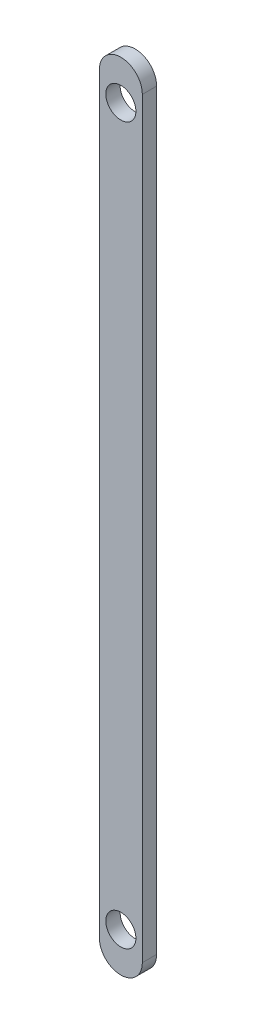
SolidWorks part; units mm, degrees
material "5052-O"
ref_plane "前基準面" through (0, 0, 0) normal (0, 0, 1) x (1, 0, 0)
ref_plane "上基準面" through (0, 0, 0) normal (0, 1, 0) x (1, 0, 0)
ref_plane "右基準面" through (0, 0, 0) normal (1, 0, 0) x (0, 0, -1)
sketch "草圖1" plane through (0, 0, 0) normal (0, 0, 1) x (1, 0, 0)
  line L0 (-3, -52.5) -> (-3, 52.5)
  line L1 (3, -52.5) -> (3, 52.5)
  line L2 (-3, 0) -> (3, 0) construction
  arc A0 (-3, 52.5) -> (3, 52.5) centre (0, 52.5) cw
  arc A1 (-3, -52.5) -> (3, -52.5) centre (0, -52.5) ccw
  dimension "D4" = 3
  dimension "D1" = 6
  dimension "D2" = 105
extrude "填料-伸長1" add sketch "草圖1" along normal blind 2
sketch "草圖2" plane through (0, 0, 2) normal (0, 0, 1) x (1, 0, 0)
  line L0 (0, 50) -> (0, -50) construction
  circle A0 centre (0, 50) radius 2.1
  circle A1 centre (0, -50) radius 2.1
  dimension "D2" = 4.2
  dimension "D1" = 100
extrude "除料-伸長1" cut sketch "草圖2" against normal through all
